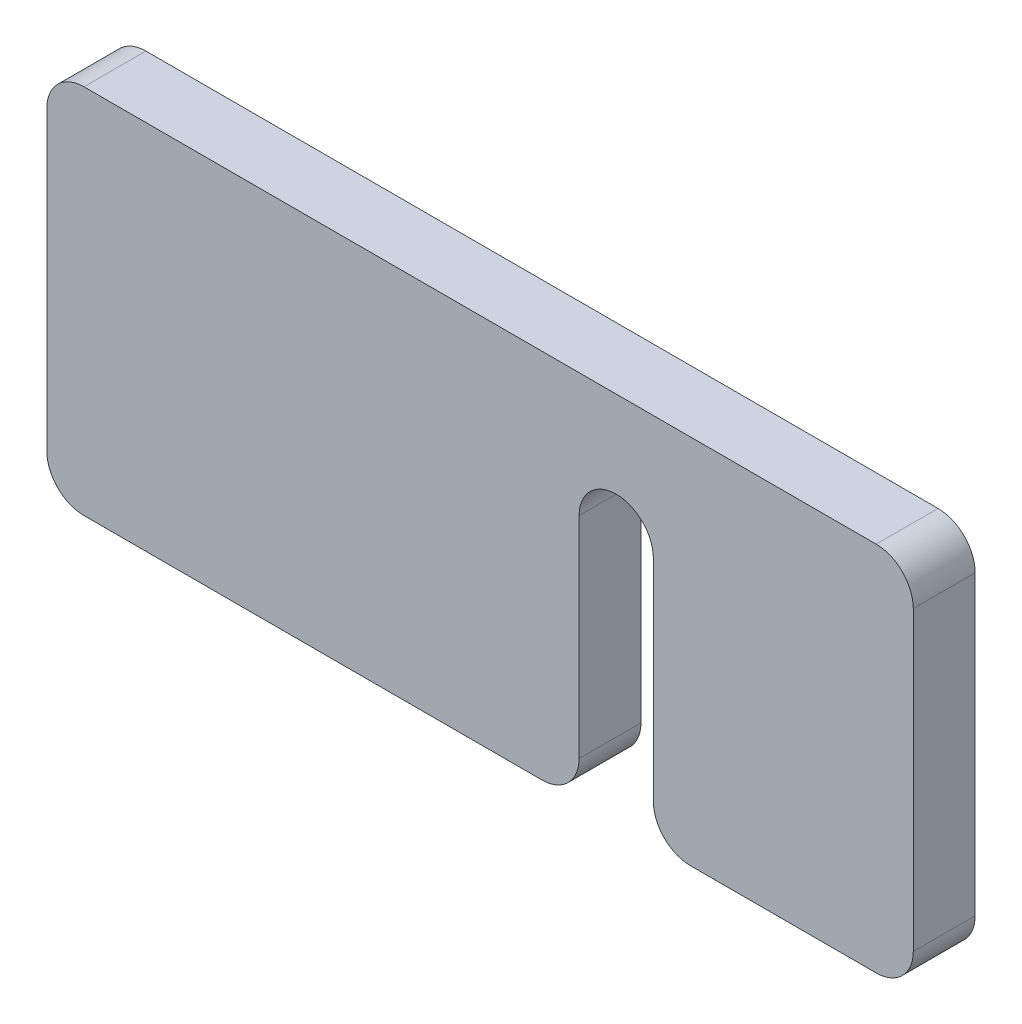
SolidWorks part; units mm, degrees
ref_plane "Plan de face" through (0, 0, 0) normal (0, 0, 1) x (1, 0, 0)
ref_plane "Plan de dessus" through (0, 0, 0) normal (0, 1, 0) x (1, 0, 0)
ref_plane "Plan de droite" through (0, 0, 0) normal (1, 0, 0) x (0, 0, -1)
sketch "Esquisse1" plane through (0, 0, 0) normal (0, 0, 1) x (1, 0, 0)
  line L0 (-35, 0) -> (35, 0)
other "Elément mécano-soudé1"
ref_plane "Plan1" through (-35, 0, 0) normal (1, 0, 0) x (0, 1, 0)
sketch "plat" plane through (-35, 0, 0) normal (1, 0, 0) x (0, 1, 0)
  line L0 (-15, 0) -> (15, 0) construction
  line L1 (-15, 2.5) -> (15, 2.5)
  line L2 (-15, 2.5) -> (-15, -2.5)
  line L3 (-15, -2.5) -> (15, -2.5)
  line L4 (15, 2.5) -> (15, -2.5)
  line L5 (0, 2.5) -> (0, -2.5) construction
  point P8 (0, 0)
  dimension "B" = 30
  dimension "A" = 5
sketch "Esquisse2" plane through (0, 0, -2.5) normal (0, 0, -1) x (-1, 0, 0)
  line L0 (-35, -15) -> (35, -15) construction
  line L1 (-14, -15) -> (-8, -15)
  line L2 (-14, -15) -> (-14, 5)
  line L4 (-8, -15) -> (-8, 5)
  line L5 (-35, -15) -> (-35, 15) construction
  arc A0 (-14, 5) -> (-8, 5) centre (-11, 5) cw
  dimension "D1" = 6
  dimension "D2" = 20
  dimension "D3" = 21
extrude "Enlèv. mat.-Extru.1" cut sketch "Esquisse2" against normal through all
fillet "Congé1" radius 3 6 edges at (8, -15, 0) (14, -15, 0) (35, -15, 0) (35, 15, 0) (-35, 15, 0) (-35, -15, 0)
